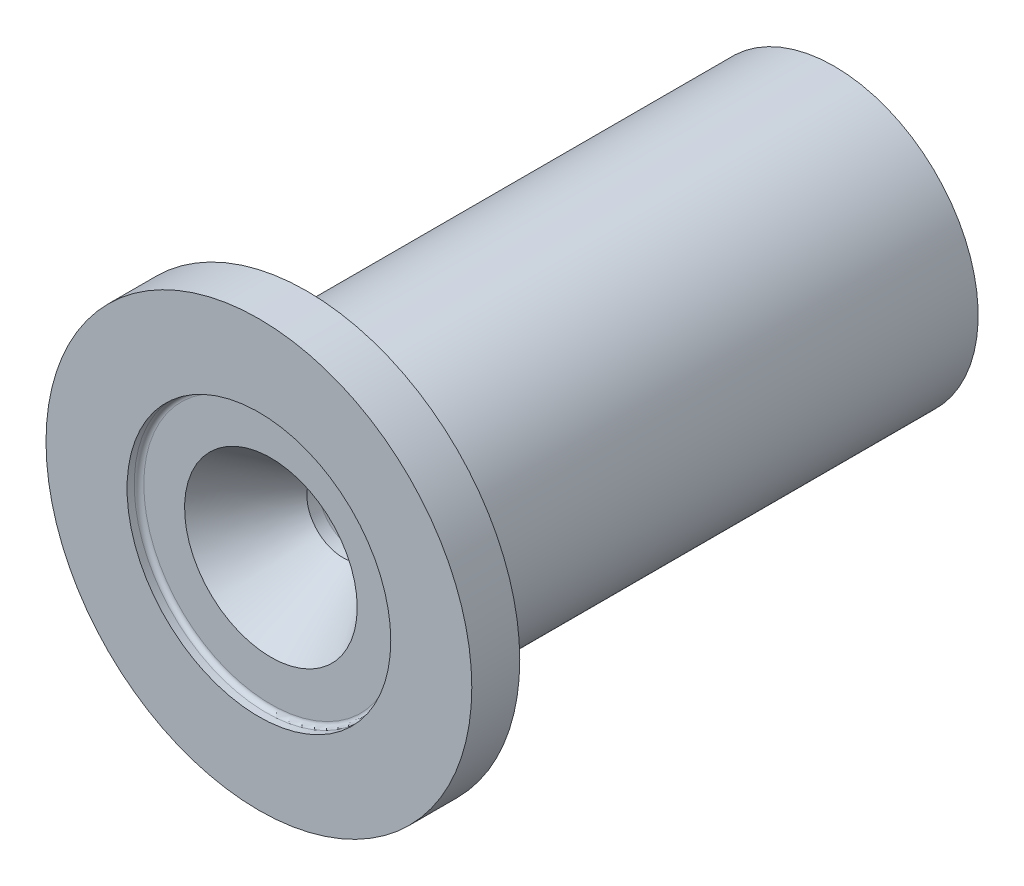
SolidWorks part; units mm, degrees
ref_plane "Front Plane" through (0, 0, 0) normal (0, 0, 1) x (1, 0, 0)
ref_plane "Top Plane" through (0, 0, 0) normal (0, 1, 0) x (1, 0, 0)
ref_plane "Right Plane" through (0, 0, 0) normal (1, 0, 0) x (0, 0, -1)
sketch "Sketch1" plane through (0, 0, 0) normal (1, 0, 0) x (0, 0, -1)
  line L0 (-76.2, 0) -> (76.2, 0) construction
  line L1 (-76.2, 25.0871) -> (-53.975, 9.525)
  line L2 (-53.975, 9.525) -> (-50.8, 9.525)
  line L3 (-50.8, 9.525) -> (76.2, 31.9185)
  line L4 (76.2, 31.9185) -> (76.2, 38.1)
  line L5 (76.2, 38.1) -> (-63.5, 38.1)
  line L6 (-63.5, 38.1) -> (-63.5, 56.388)
  line L7 (-63.5, 56.388) -> (-76.2, 56.388)
  line L8 (-76.2, 56.388) -> (-76.2, 25.0871)
  point P9 (0, 0)
  point P12 (0, 0)
  dimension "D1" = 12.7
  dimension "D2" = 152.4
  dimension "D3" = 127
  dimension "D4" = 9.525
  dimension "D5" = 10
  dimension "D6" = 56.388
  dimension "D7" = 35
  dimension "D8" = 3.175
  dimension "D9" = 38.1
revolve "Revolve1" add sketch "Sketch1" angle 360 about L0
fillet "Fillet1" radius 6.35 1 edges at (0, -38.1, 63.5)
sketch "Sketch2" plane through (0, 0, 76.2) normal (0, 0, 1) x (1, 0, 0)
  circle A0 centre (0, 0) radius 34.925
  dimension "D1" = 69.85
extrude "Cut-Extrude1" cut sketch "Sketch2" against normal blind 3.175
fillet "Fillet2" radius 1.27 1 edges at (34.925, 0, 73.025)
